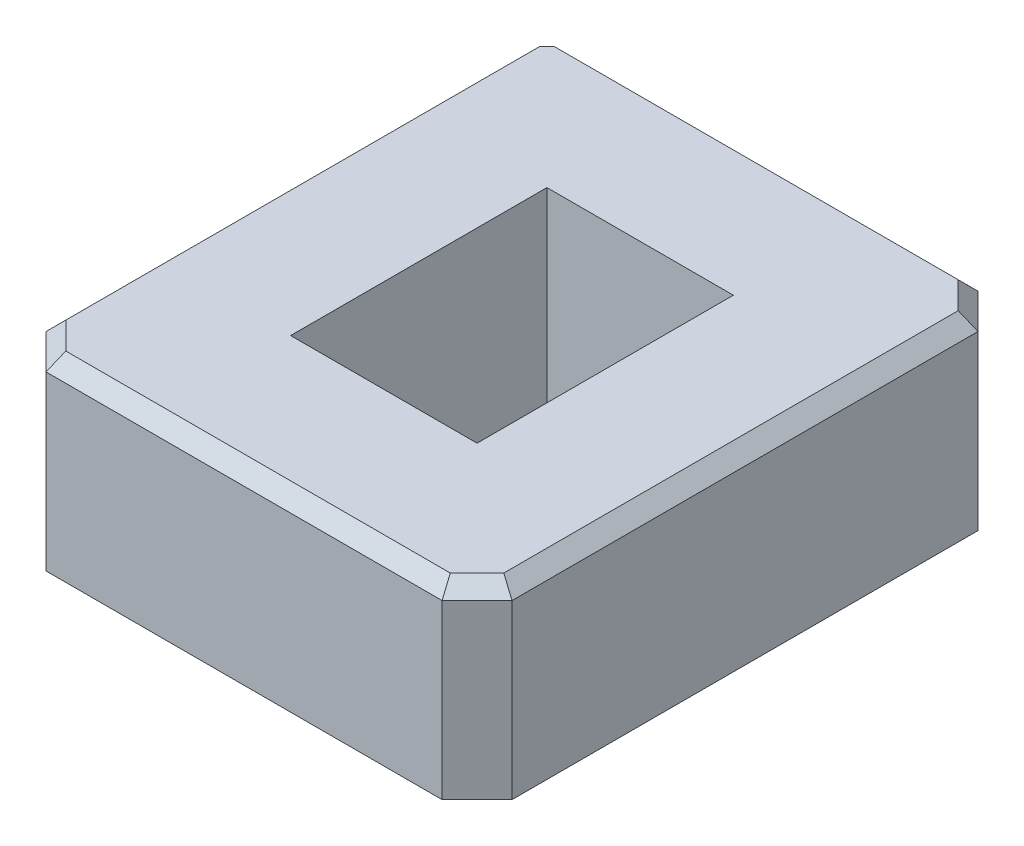
SolidWorks part; units mm, degrees
ref_plane "Front" through (0, 0, 0) normal (0, 0, 1) x (1, 0, 0)
ref_plane "Top" through (0, 0, 0) normal (0, 1, 0) x (1, 0, 0)
ref_plane "Right" through (0, 0, 0) normal (1, 0, 0) x (0, 0, -1)
sketch "Sketch1" plane through (0, 0, 0) normal (0, 1, 0) x (1, 0, 0)
  line L0 (-10, 11.5) -> (10, 11.5)
  line L1 (-4, -5.5) -> (4, -5.5)
  line L2 (-4, -5.5) -> (-4, 5.5)
  line L3 (-4, 5.5) -> (4, 5.5)
  line L4 (4, -5.5) -> (4, 5.5)
  line L5 (-4, -5.5) -> (4, 5.5) construction
  line L6 (-4, 5.5) -> (4, -5.5) construction
  line L7 (10, -11.5) -> (10, 11.5)
  line L8 (-10, -11.5) -> (10, -11.5)
  line L9 (-10, -11.5) -> (-10, 11.5)
  point P0 (0, 0)
  dimension "D1" = 11
  dimension "D2" = 8
  dimension "D3" = 6
extrude "Boss-Extrude1" add sketch "Sketch1" along normal blind 8
chamfer "Chamfer1" distance 1.5 angle 45 4 edges at (10, 4, 11.5) (10, 4, -11.5) (-10, 4, -11.5) (-10, 4, 11.5)
chamfer "Chamfer2" distance 0.6 angle 45 7 edges at (0, 8, -11.5) (9.25, 8, -10.75) (10, 8, 0) (9.25, 8, 10.75) (0, 8, 11.5) (-9.25, 8, 10.75) (-10, 8, 0)
